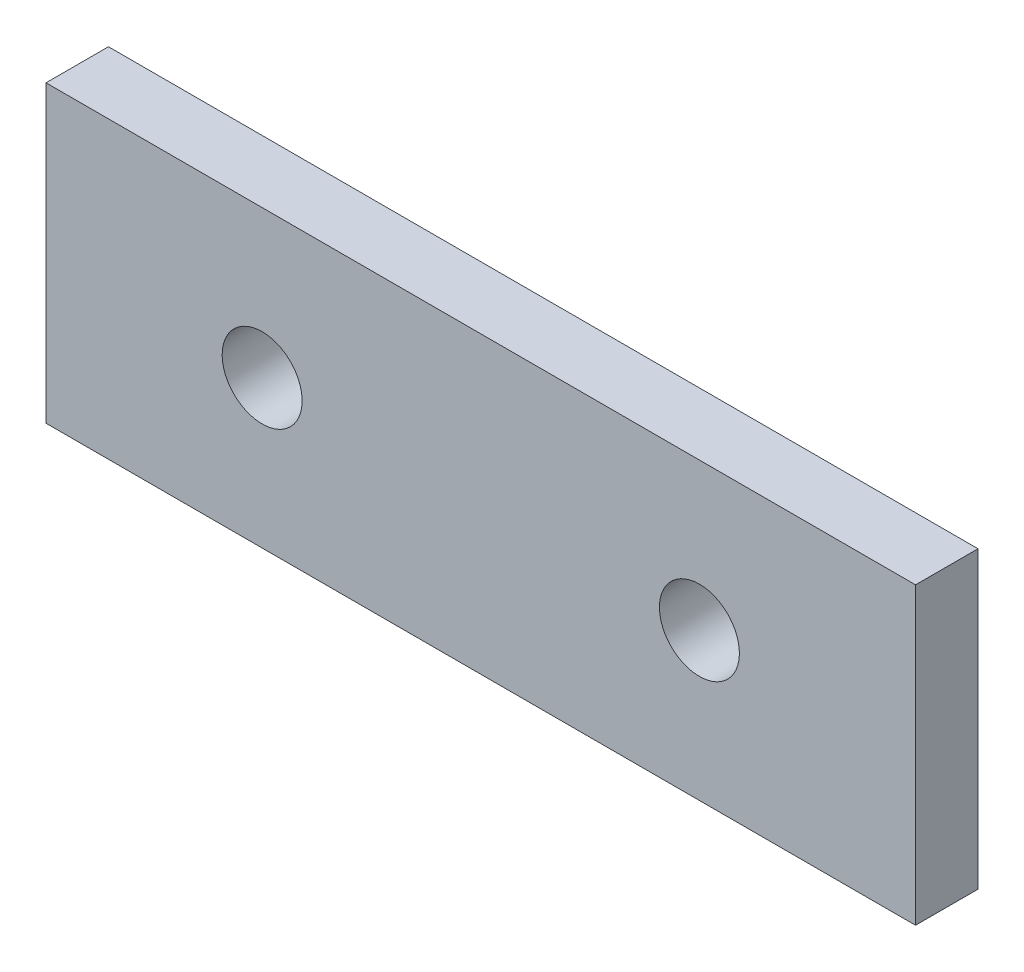
SolidWorks part; units mm, degrees
ref_plane "Alzado" through (0, 0, 0) normal (0, 0, 1) x (1, 0, 0)
ref_plane "Planta" through (0, 0, 0) normal (0, 1, 0) x (1, 0, 0)
ref_plane "Vista lateral" through (0, 0, 0) normal (1, 0, 0) x (0, 0, -1)
sketch "Croquis1" plane through (0, 0, 0) normal (0, 0, 1) x (1, 0, 0)
  line L0 (17.4, -29.9) -> (17.4, -18.1)
  line L1 (17.4, -18.1) -> (-17.4, -18.1)
  line L2 (-17.4, -18.1) -> (-17.4, -29.9)
  line L3 (-17.4, -29.9) -> (17.4, -29.9)
  line L4 (17.5, -30) -> (17.5, -18)
  line L5 (17.5, -18) -> (-17.5, -18)
  line L6 (-17.5, -18) -> (-17.5, -30)
  line L7 (-17.5, -30) -> (17.5, -30)
  line L8 (17.5, -30) -> (17.5, -18)
  line L9 (17.5, -18) -> (-17.5, -18)
  line L10 (-17.5, -18) -> (-17.5, -30)
  line L11 (-17.5, -30) -> (17.5, -30)
  circle A0 centre (-8.75, -24) radius 1.6 construction
  circle A1 centre (8.75, -24) radius 1.6 construction
  circle A2 centre (-8.75, -24) radius 1.6
  circle A3 centre (8.75, -24) radius 1.6
  dimension "D1" = 0
  dimension "D2" = 0.1
extrude "Saliente-Extruir1" add sketch "Croquis1" along normal up to surface (2.5 mm away) contours L2 L3 L0 L1 A3 A2
